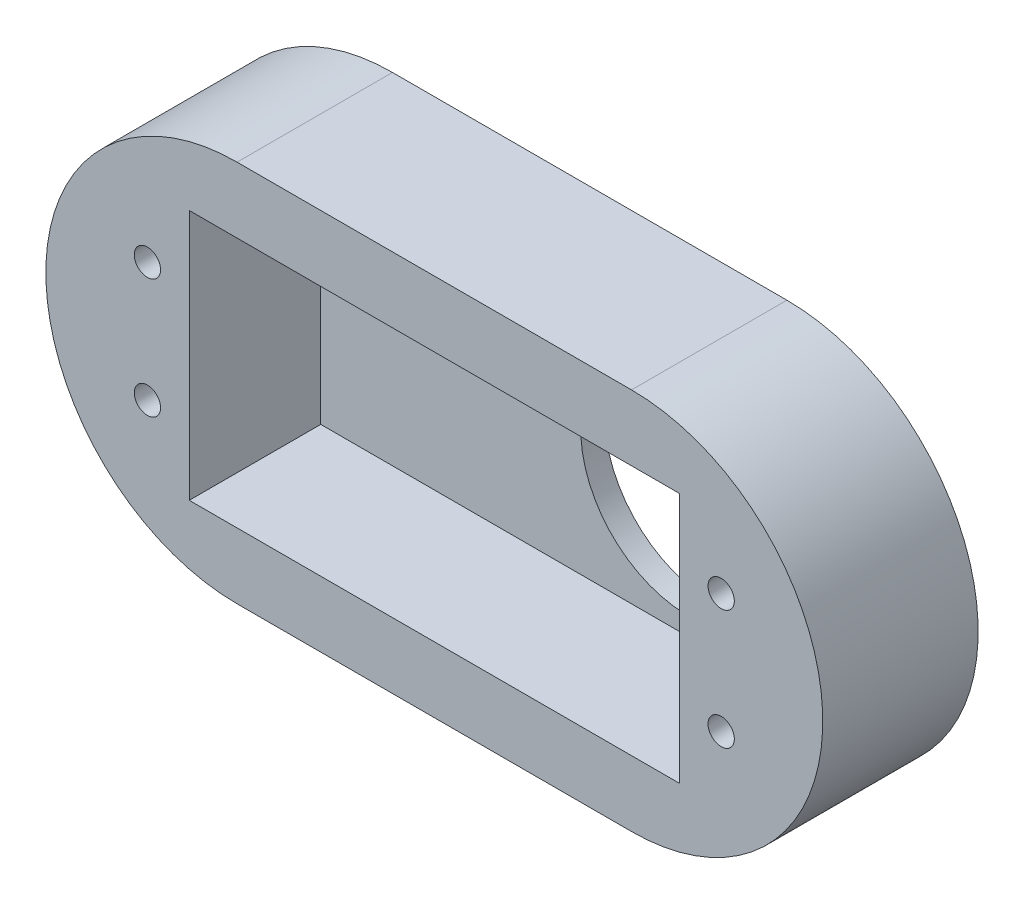
SolidWorks part; units mm, degrees
ref_plane "Front Plane" through (0, 0, 0) normal (0, 0, 1) x (1, 0, 0)
ref_plane "Top Plane" through (0, 0, 0) normal (0, 1, 0) x (1, 0, 0)
ref_plane "Right Plane" through (0, 0, 0) normal (1, 0, 0) x (0, 0, -1)
sketch "Sketch1" plane through (0, 0, 0) normal (0, 0, 1) x (1, 0, 0)
  line L0 (-3.5, 15.5) -> (-3.5, 5.5) construction
  line L1 (0, 0) -> (41, 0)
  line L2 (0, 0) -> (0, 21)
  line L3 (0, 21) -> (41, 21)
  line L4 (41, 0) -> (41, 21)
  line L5 (4, -5.5) -> (37, -5.5)
  line L6 (4, -5.5) -> (4, 26.5) construction
  line L7 (4, 26.5) -> (37, 26.5)
  line L8 (37, -5.5) -> (37, 26.5) construction
  arc A0 (37, -5.5) -> (37, 26.5) centre (37, 10.5) ccw
  arc A1 (4, 26.5) -> (4, -5.5) centre (4, 10.5) ccw
  circle A2 centre (-3.5, 15.5) radius 1.1
  circle A3 centre (-3.5, 5.5) radius 1.1
  circle A4 centre (44.5, 5.5) radius 1.1
  circle A5 centre (44.5, 15.5) radius 1.1
  point P9 (20.5, 26.5)
  point P10 (20.5, 21)
  point P11 (4, 10.5)
  point P12 (0, 10.5)
  point P23 (-3.5, 10.5)
  point P24 (0, 0)
  point P25 (0, 0)
  point P26 (0, 0)
  point P27 (0, 0)
  point P28 (0, 0)
  dimension "D6" = 2.2
  dimension "D1" = 21
  dimension "D2" = 41
  dimension "D3" = 33
  dimension "D4" = 32
  dimension "D5" = 10
  dimension "D7" = 3.5
  dimension "D8" = 3.5
extrude "Boss-Extrude1" add sketch "Sketch1" along normal blind 11
sketch "Sketch2" plane through (0, 0, 0) normal (0, 0, 1) x (1, 0, 0)
  line L0 (41, 0) -> (41, 21) construction
  line L1 (41, 0) -> (41, 21) construction
  line L2 (37, 26.5) -> (4, 26.5)
  line L3 (4, -5.5) -> (37, -5.5)
  line L4 (37, 26.5) -> (4, 26.5)
  line L5 (4, -5.5) -> (37, -5.5)
  line L6 (39.75, 10.5) -> (41, 10.5) construction
  circle A0 centre (30.75, 10.5) radius 9
  arc A2 (4, 26.5) -> (4, -5.5) centre (4, 10.5) ccw
  arc A3 (37, -5.5) -> (37, 26.5) centre (37, 10.5) ccw
  arc A4 (4, 26.5) -> (4, -5.5) centre (4, 10.5) ccw
  arc A5 (37, -5.5) -> (37, 26.5) centre (37, 10.5) ccw
  dimension "D2" = 18
  dimension "D3" = 1.25
  dimension "D1" = 0
extrude "Boss-Extrude2" add sketch "Sketch2" against normal blind 2
